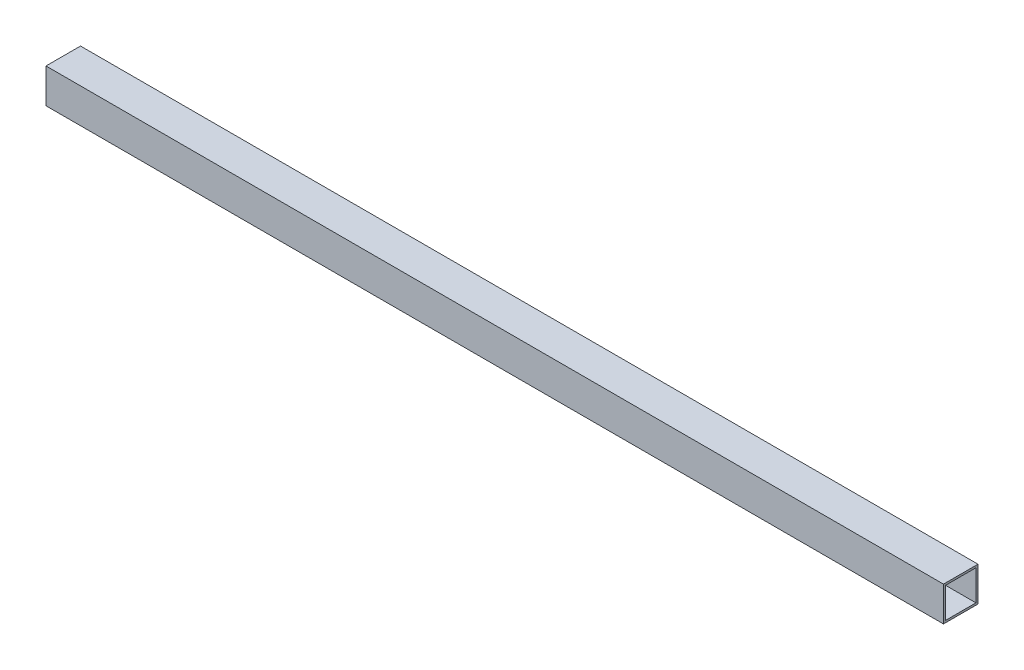
SolidWorks part; units mm, degrees
material "6061 Alloy"
ref_plane "Front Plane" through (0, 0, 0) normal (0, 0, 1) x (1, 0, 0)
ref_plane "Top Plane" through (0, 0, 0) normal (0, 1, 0) x (1, 0, 0)
ref_plane "Right Plane" through (0, 0, 0) normal (1, 0, 0) x (0, 0, -1)
sketch "Sketch1" plane through (0, 0, 0) normal (1, 0, 0) x (0, 0, -1)
  line L0 (-8.8, 8.8) -> (8.8, 8.8)
  line L1 (-10, -10) -> (10, -10)
  line L2 (-10, -10) -> (-10, 10)
  line L3 (-10, 10) -> (10, 10)
  line L4 (10, -10) -> (10, 10)
  line L5 (-10, -10) -> (10, 10) construction
  line L6 (-10, 10) -> (10, -10) construction
  line L7 (8.8, -8.8) -> (8.8, 8.8)
  line L8 (-8.8, -8.8) -> (8.8, -8.8)
  line L9 (-8.8, -8.8) -> (-8.8, 8.8)
  point P0 (0, 0)
  dimension "D1" = 20
  dimension "D2" = 20
  dimension "D3" = 1.2
extrude "Boss-Extrude1" add sketch "Sketch1" along normal blind 520
